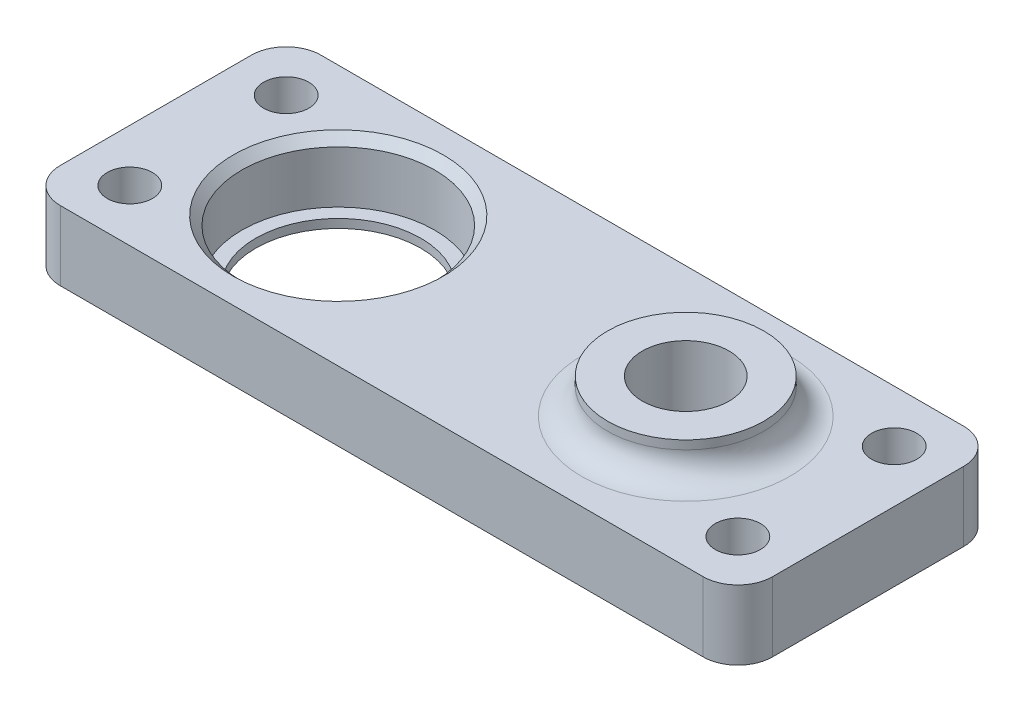
SolidWorks part; units mm, degrees
ref_plane "Front Plane" through (0, 0, 0) normal (0, 0, 1) x (1, 0, 0)
ref_plane "Top Plane" through (0, 0, 0) normal (0, 1, 0) x (1, 0, 0)
ref_plane "Right Plane" through (0, 0, 0) normal (1, 0, 0) x (0, 0, -1)
sketch "Sketch1" plane through (0, 0, 0) normal (0, 1, 0) x (1, 0, 0)
  line L0 (-17, 15) -> (57, 15)
  line L1 (-17, -15) -> (57, -15)
  line L2 (-21, 11) -> (-21, -11)
  line L3 (61, 11) -> (61, -11)
  line L4 (40, 0) -> (61, 0) construction
  circle A0 centre (0, 0) radius 9.5
  circle A1 centre (40, 0) radius 5
  circle A2 centre (-15, 9) radius 2.6
  circle A3 centre (-15, -9) radius 2.6
  circle A4 centre (55, 9) radius 2.6
  circle A5 centre (55, -9) radius 2.6
  arc A6 (57, 15) -> (61, 11) centre (57, 11) cw
  arc A7 (57, -15) -> (61, -11) centre (57, -11) ccw
  arc A8 (-17, -15) -> (-21, -11) centre (-17, -11) cw
  arc A9 (-17, 15) -> (-21, 11) centre (-17, 11) ccw
  point P20 (61, 15)
  point P23 (61, -15)
  dimension "D2" = 19
  dimension "D3" = 10
  dimension "D6" = 18
  dimension "D7" = 30
  dimension "D8" = 5.2
  dimension "D12" = 4
  dimension "D1" = 40
  dimension "D4" = 15
  dimension "D5" = 15
  dimension "D9" = 9
  dimension "D10" = 6
  dimension "D11" = 6
extrude "Boss-Extrude1" add sketch "Sketch1" along normal blind 8
sketch "Sketch2" plane through (0, 8, 0) normal (0, 1, 0) x (1, 0, 0)
  circle A0 centre (0, 0) radius 11.1
  dimension "D1" = 22.2
extrude "Cut-Extrude1" cut sketch "Sketch2" against normal blind 7
sketch "Sketch3" plane through (0, 8, 0) normal (0, 1, 0) x (1, 0, 0)
  circle A0 centre (40, 0) radius 9
  circle A1 centre (40, 0) radius 5 construction
  circle A2 centre (40, 0) radius 5
  dimension "D1" = 18
extrude "Boss-Extrude2" add sketch "Sketch3" along normal blind 4
fillet "Fillet1" radius 3 1 edges at (40, 8, -9)
chamfer "Chamfer1" distance 1 angle 45 1 edges at (0, 8, 11.1)
